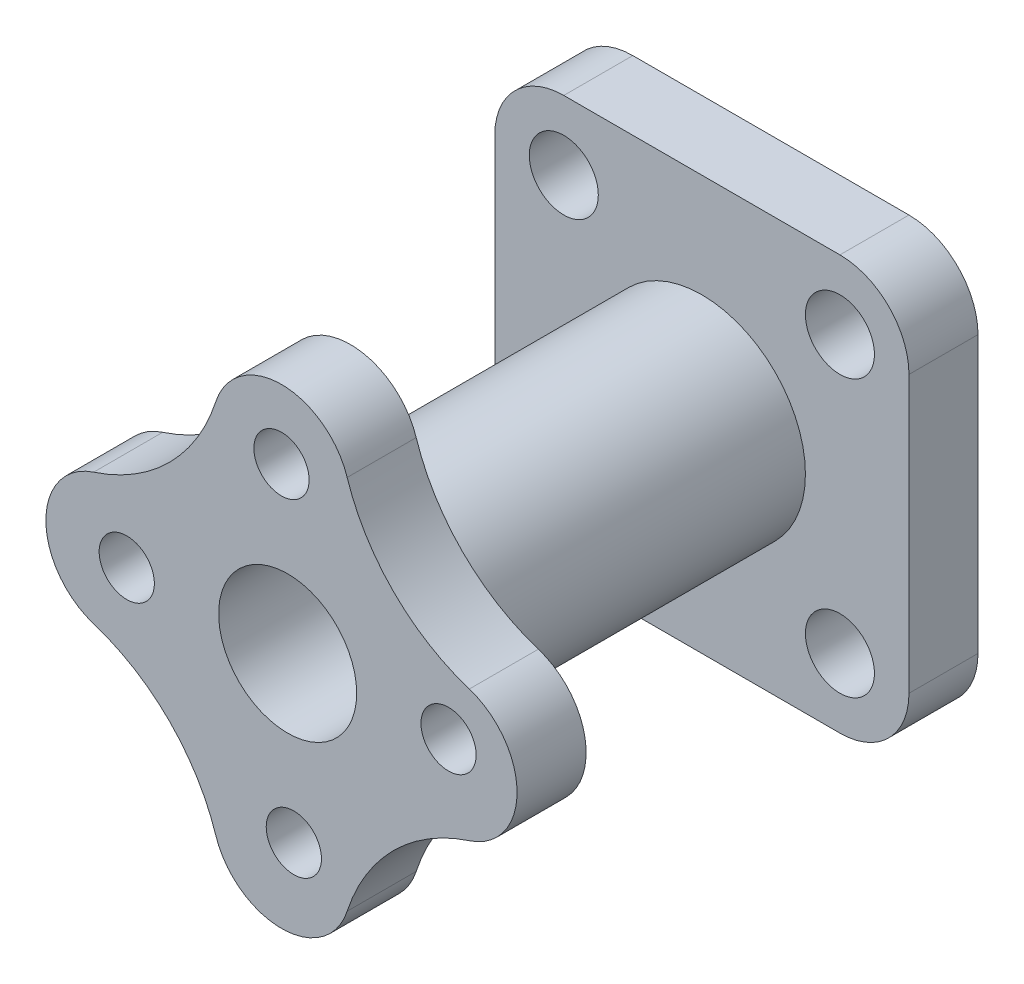
SolidWorks part; units mm, degrees
ref_plane "Piano frontale" through (0, 0, 0) normal (0, 0, 1) x (1, 0, 0)
ref_plane "Piano superiore" through (0, 0, 0) normal (0, 1, 0) x (1, 0, 0)
ref_plane "Piano destro" through (0, 0, 0) normal (1, 0, 0) x (0, 0, -1)
sketch "Schizzo1" plane through (0, 0, 0) normal (0, 0, 1) x (1, 0, 0)
  line L1 (-60, 60) -> (60, 60)
  line L2 (-60, 60) -> (-60, -60)
  line L3 (-60, -60) -> (60, -60)
  line L4 (60, 60) -> (60, -60)
  dimension "D1" = 120
  dimension "D2" = 120
  dimension "D3" = 60
  dimension "D4" = 60
extrude "Estrusione-Estrusione1" add sketch "Schizzo1" along normal blind 20
sketch "Schizzo3" plane through (0, 0, 20) normal (0, 0, 1) x (1, 0, 0)
  circle A0 centre (0, 0) radius 30
  circle A1 centre (0, 0) radius 20
  dimension "D1" = 60
  dimension "D2" = 40
extrude "Estrusione-Estrusione2" add sketch "Schizzo3" along normal blind 100
sketch "Schizzo4" plane through (0, 0, 120) normal (0, 0, 1) x (1, 0, 0)
  circle A0 centre (0, 0) radius 20 construction
  circle A1 centre (0, 0) radius 20
  arc A8 (-56.2055, 17.3834) -> (-20.8161, 52.7728) centre (-73.1431, 69.7104) ccw
  arc A9 (17.2399, 52.7728) -> (52.6294, 17.3834) centre (69.5669, 69.7104) ccw
  arc A10 (52.6294, -20.6726) -> (17.2399, -56.062) centre (69.5669, -72.9996) ccw
  arc A11 (-20.8161, -56.062) -> (-56.2055, -20.6726) centre (-73.1431, -72.9996) ccw
  arc A13 (17.2399, 52.7728) -> (-20.8161, 52.7728) centre (-1.7881, 46.6137) ccw
  arc A15 (52.6294, -20.6726) -> (52.6294, 17.3834) centre (46.4702, -1.6446) ccw
  arc A16 (-20.8161, -56.062) -> (17.2399, -56.062) centre (-1.7881, -49.9029) ccw
  arc A17 (-56.2055, 17.3834) -> (-56.2055, -20.6726) centre (-50.0464, -1.6446) ccw
  point P14 (-1.7881, -1.6446)
  point P22 (0, 0)
  dimension "D1" = 4
  dimension "D2" = 110
extrude "Estrusione-Estrusione3" add sketch "Schizzo4" along normal blind 20
fillet "Raccordo2" radius 20 4 edges at (60, 60, 10) (60, -60, 10) (-60, 60, 10) (-60, -60, 10)
sketch "Schizzo7" plane through (0, 0, 0) normal (0, 0, -1) x (-1, 0, 0)
  circle A0 centre (-40, 40) radius 10
  arc A1 (-40, 60) -> (-60, 40) centre (-40, 40) ccw construction
  dimension "D1" = 20
  dimension "D2" = 0
sketch "Schizzo8" plane through (0, 0, 140) normal (0, 0, 1) x (1, 0, 0)
  circle A0 centre (-1.7881, 46.6137) radius 8
  point P3 (0, 0)
extrude "Taglio-Estrusione1" cut sketch "Schizzo8" against normal up to next (20 mm away)
extrude "Taglio-Estrusione2" cut sketch "Schizzo7" against normal up to next (20 mm away) contours A0
pattern_circular "RipetizioneCircolare1" count 4 over 360 about axis through (0, 0, 0) along (0, 0, 1) of "Taglio-Estrusione2", "Taglio-Estrusione1"
